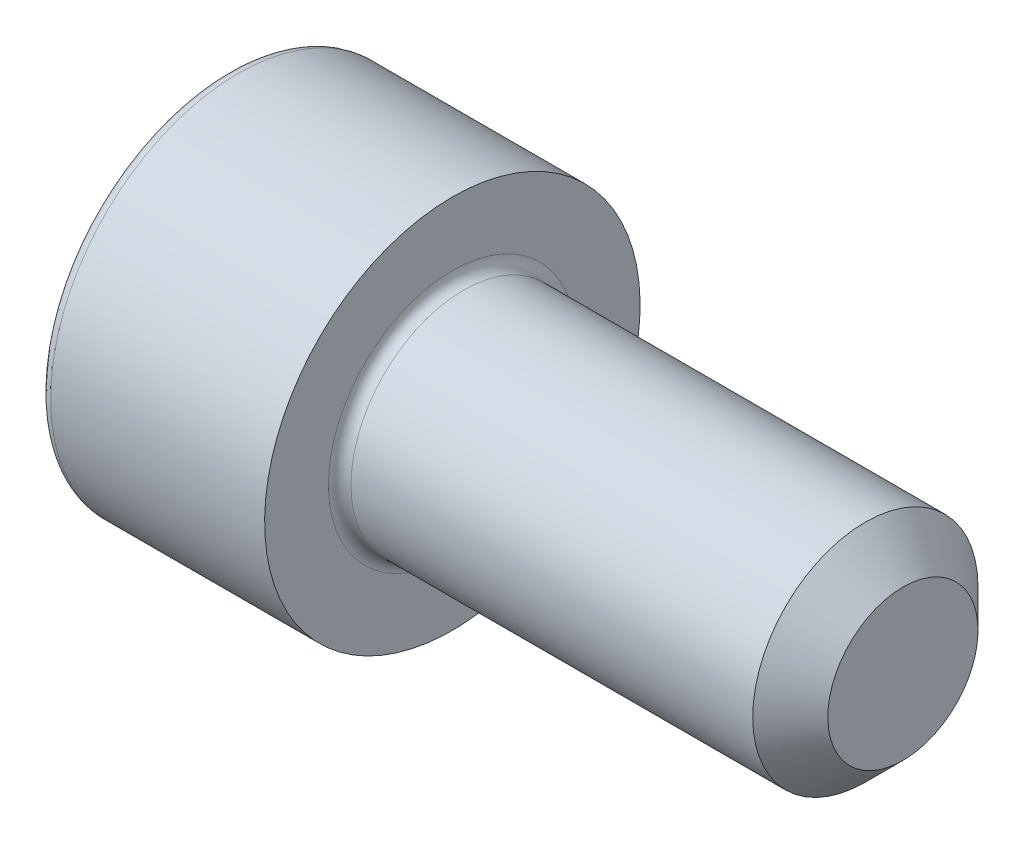
SolidWorks part; units mm, degrees
ref_plane "Спереди" through (0, 0, 0) normal (0, 0, 1) x (1, 0, 0)
ref_plane "Сверху" through (0, 0, 0) normal (0, 1, 0) x (1, 0, 0)
ref_plane "Справа" through (0, 0, 0) normal (1, 0, 0) x (0, 0, -1)
sketch "Эскиз1" plane through (0, 0, 0) normal (0, 0, 1) x (1, 0, 0)
  line L0 (0, 0) -> (0, 5)
  line L1 (0, 5) -> (6, 5)
  line L2 (6, 5) -> (6, 3)
  line L3 (6, 3) -> (18, 3)
  line L4 (18, 3) -> (18, 0)
  line L5 (18, 0) -> (0, 0) construction
  line L6 (0, 0) -> (18, 0)
  dimension "D1" = 10
  dimension "D2" = 6
  dimension "D3" = 6
  dimension "D4" = 12
revolve "Повернуть1" add sketch "Эскиз1" angle 360 about L5
cosmetic thread "Условное изображение резьбы1" parameters "D2"=4.891
sketch "Эскиз2" plane through (0, 0, 0) normal (-1, 0, 0) x (0, 0, 1)
  line L1 (-1.4434, 2.5) -> (-2.8868, 0)
  line L2 (-2.8868, 0) -> (-1.4434, -2.5)
  line L3 (-1.4434, -2.5) -> (1.4434, -2.5)
  line L4 (1.4434, -2.5) -> (2.8868, 0)
  line L5 (2.8868, 0) -> (1.4434, 2.5)
  line L6 (1.4434, 2.5) -> (-1.4434, 2.5)
  circle A0 centre (0, 0) radius 2.5 construction
  dimension "D1" = 5
extrude "Вырез-Вытянуть1" cut sketch "Эскиз2" against normal blind 2.5
fillet "Скругление1" radius 0.3 2 edges at (0, 5, 0) (6, 3, 0)
chamfer "Фаска1" distance 1 angle 45 1 edges at (18, 3, 0)
